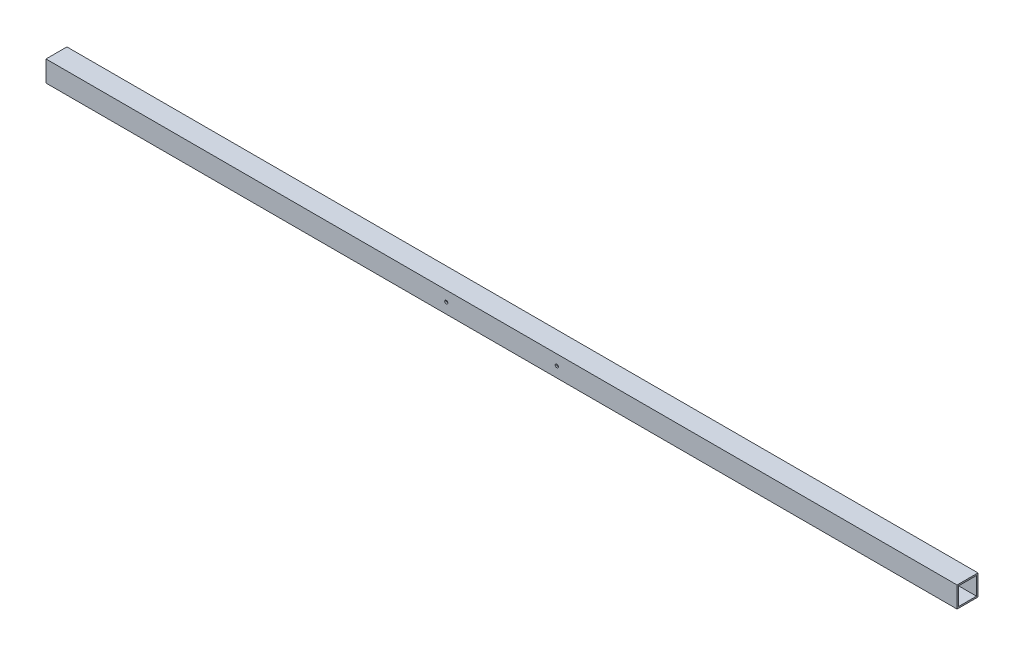
SolidWorks part; units mm, degrees
material "6061 Alloy"
ref_plane "Front Plane" through (0, 0, 0) normal (0, 0, 1) x (1, 0, 0)
ref_plane "Top Plane" through (0, 0, 0) normal (0, 1, 0) x (1, 0, 0)
ref_plane "Right Plane" through (0, 0, 0) normal (1, 0, 0) x (0, 0, -1)
sketch "Sketch1" plane through (0, 0, 0) normal (1, 0, 0) x (0, 0, -1)
  line L1 (0, 0) -> (44.45, 0)
  line L2 (0, 0) -> (0, 44.45)
  line L3 (0, 44.45) -> (44.45, 44.45)
  line L4 (44.45, 0) -> (44.45, 44.45)
  line L5 (3.175, 41.275) -> (41.275, 41.275)
  line L6 (3.175, 41.275) -> (3.175, 3.175)
  line L7 (3.175, 3.175) -> (41.275, 3.175)
  line L8 (41.275, 41.275) -> (41.275, 3.175)
  dimension "D1" = 44.45
  dimension "D2" = 38.1
  dimension "D3" = 3.175
  dimension "D4" = 44.45
  dimension "D5" = 38.1
  dimension "D6" = 3.175
extrude "Boss-Extrude1" add sketch "Sketch1" along normal blind 1936.75
hole_wizard "17/64 (0.26563) Diameter Hole1" positions "Sketch2" profile "Sketch3" hole size "17/64" standard "ANSI Inch" end condition through all
sketch "Sketch2" plane through (0, 0, 0) normal (0, 0, 1) x (1, 0, 0)
  line L0 (968.375, 44.45) -> (968.375, 0) construction
  line L1 (1936.75, 44.45) -> (0, 44.45) construction
  line L2 (1936.75, 0) -> (0, 0) construction
  point P0 (850.9, 22.225)
  point P2 (1085.85, 22.225)
  dimension "D1" = 234.95
  dimension "D2" = 22.225
  dimension "D3" = 117.475
sketch "Sketch3" plane through (850.9, 22.225, 0) normal (1, 0, 0) x (0, -1, 0)
  line L0 (0, 0) -> (0, 44.45)
  line L1 (0, 44.45) -> (3.3735, 44.45)
  line L2 (3.3735, 44.45) -> (3.3735, 0)
  line L5 (3.3735, 0) -> (0, 0)
  line L11 (0, -6.35) -> (0, 107.95) construction
  dimension "Thru Hole Dia." = 6.747
  dimension "Thru Hole Depth" = 44.45
equation "\"D3@Sketch2\"=\"D1@Sketch2\"/2"
